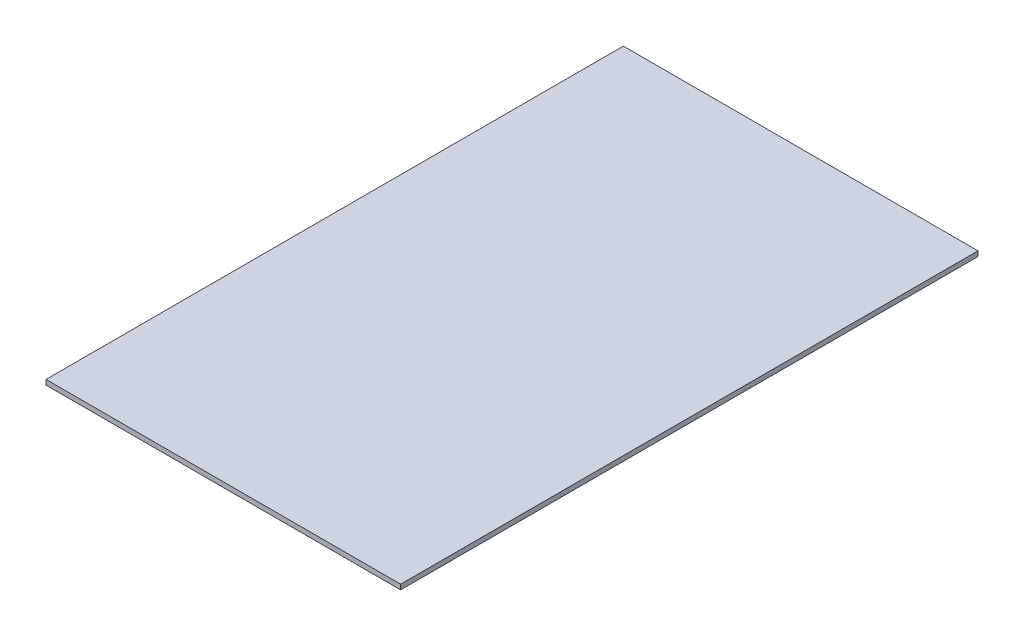
SolidWorks part; units mm, degrees
ref_plane "Front Plane" through (0, 0, 0) normal (0, 0, 1) x (1, 0, 0)
ref_plane "Top Plane" through (0, 0, 0) normal (0, 1, 0) x (1, 0, 0)
ref_plane "Right Plane" through (0, 0, 0) normal (1, 0, 0) x (0, 0, -1)
sketch "Sketch1" plane through (0, -10, 0) normal (0, -1, 0) x (1, 0, 0)
  line L1 (-107.5, 227.5) -> (107.5, 227.5)
  line L2 (-107.5, 227.5) -> (-107.5, -122.5)
  line L3 (-107.5, -122.5) -> (107.5, -122.5)
  line L4 (107.5, 227.5) -> (107.5, -122.5)
extrude "Boss-Extrude1" add sketch "Sketch1" along normal blind 3
